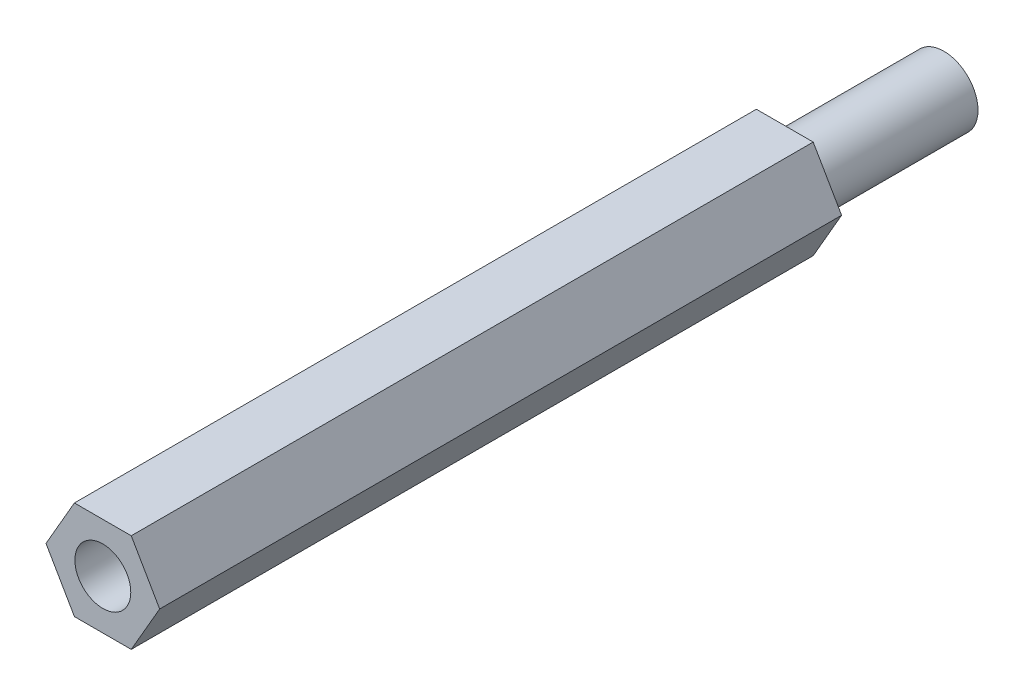
SolidWorks part; units mm, degrees
material "201 ricotto (SS)"
ref_plane "Piano frontale" through (0, 0, 0) normal (0, 0, 1) x (1, 0, 0)
ref_plane "Piano superiore" through (0, 0, 0) normal (0, 1, 0) x (1, 0, 0)
ref_plane "Piano destro" through (0, 0, 0) normal (1, 0, 0) x (0, 0, -1)
sketch "Schizzo1" plane through (0, 0, 0) normal (0, 0, 1) x (1, 0, 0)
  line L0 (1.25, -2.1651) -> (2.5, 0)
  line L1 (2.5, 0) -> (1.25, 2.1651)
  line L2 (1.25, 2.1651) -> (-1.25, 2.1651)
  line L3 (-1.25, 2.1651) -> (-2.5, 0)
  line L4 (-2.5, 0) -> (-1.25, -2.1651)
  line L5 (-1.25, -2.1651) -> (1.25, -2.1651)
extrude "Estrusione-Estrusione1" add sketch "Schizzo1" against normal blind 30
sketch "Schizzo2" plane through (0, 0, -30) normal (0, 0, -1) x (-1, 0, 0)
  circle A0 centre (0, 0) radius 1.5
extrude "Estrusione-Estrusione2" add sketch "Schizzo2" along normal blind 7
hole_wizard "Foro1" positions "Schizzo4" profile "Schizzo3" legacy
sketch "Schizzo4" plane through (0, 0, 0) normal (0, 0, 1) x (1, 0, 0)
  point P0 (0, 0)
sketch "Schizzo3" plane through (0, 0, 0) normal (1, 0, 0) x (0, -1, 0)
  line L0 (0, 0) -> (0, 7)
  line L1 (0, 7) -> (1.2295, 7)
  line L2 (1.2295, 7) -> (1.2295, 0)
  line L3 (1.2295, 0) -> (0, 0)
  line L4 (0, 110) -> (0, -10) construction
  dimension "Diameter" = 2.459
  dimension "Depth" = 7
equation "\"Altezza\"= 30mm"
equation "\"D1@Estrusione-Estrusione1\"=\"Altezza\""
